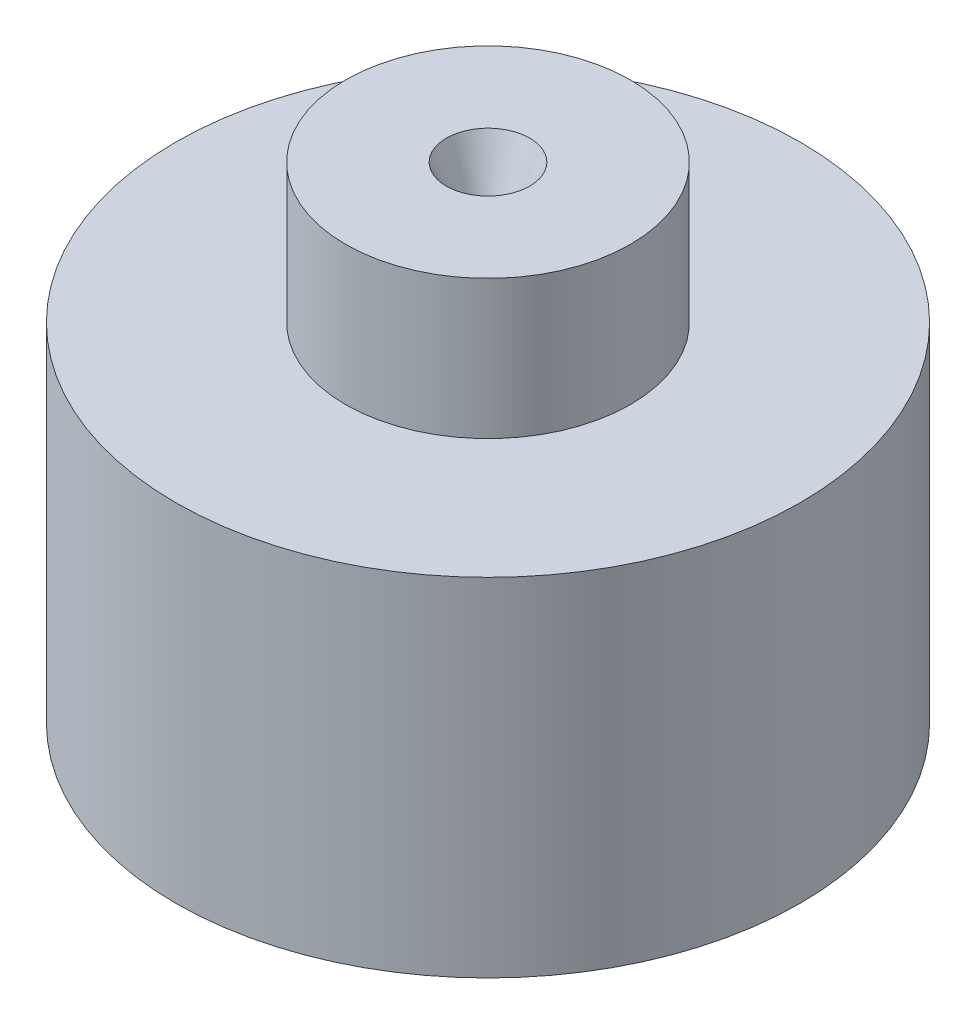
SolidWorks part; units mm, degrees
ref_plane "Front Plane" through (0, 0, 0) normal (0, 0, 1) x (1, 0, 0)
ref_plane "Top Plane" through (0, 0, 0) normal (0, 1, 0) x (1, 0, 0)
ref_plane "Right Plane" through (0, 0, 0) normal (1, 0, 0) x (0, 0, -1)
sketch "Sketch1" plane through (0, 0, 0) normal (0, 1, 0) x (1, 0, 0)
  circle A0 centre (0, 0) radius 45
extrude "Boss-Extrude1" add sketch "Sketch1" along normal blind 50
sketch "Sketch2" plane through (0, 0, 0) normal (1, 0, 0) x (0, 0, -1)
  line L0 (0, 50) -> (0, 0)
  line L1 (45, 50) -> (-45, 50) construction
  line L2 (0, 0) -> (-40, 0)
  line L3 (-45, 0) -> (45, 0) construction
  line L4 (-40, 0) -> (-40, 10)
  line L7 (-6, 50) -> (0, 50)
  line L8 (-40, 10) -> (-37, 10)
  line L9 (-37, 10) -> (-6, 41)
  line L10 (-6, 41) -> (-6, 50)
  dimension "D1" = 40
  dimension "D2" = 9
  dimension "D3" = 3
  dimension "D4" = 6
  dimension "D5" = 135
  dimension "D6" = 9
revolve "Cut-Revolve1" cut sketch "Sketch2" angle 360 about L0
sketch "Sketch3" plane through (0, 0, 0) normal (1, 0, 0) x (0, 0, -1)
  line L0 (-6, 50) -> (-20.5229, 50)
  line L1 (45, 50) -> (-45, 50) construction
  line L2 (-20.5229, 50) -> (-20.5229, 70)
  line L3 (-20.5229, 70) -> (-6, 70)
  line L4 (0, 70) -> (0, 50) construction
  line L5 (-6, 50) -> (-2.2499, 59)
  line L6 (-2.2499, 59) -> (-2.2499, 61)
  line L7 (-2.2499, 61) -> (-6, 70)
  line L8 (-6, 70) -> (0, 70) construction
  line L9 (0, 50) -> (-6, 50) construction
  dimension "D1" = 0
  dimension "D2" = 9
  dimension "D3" = 2
  dimension "D4" = 20
  dimension "D5" = 6
revolve "Revolve1" add sketch "Sketch3" angle 360 about L4
